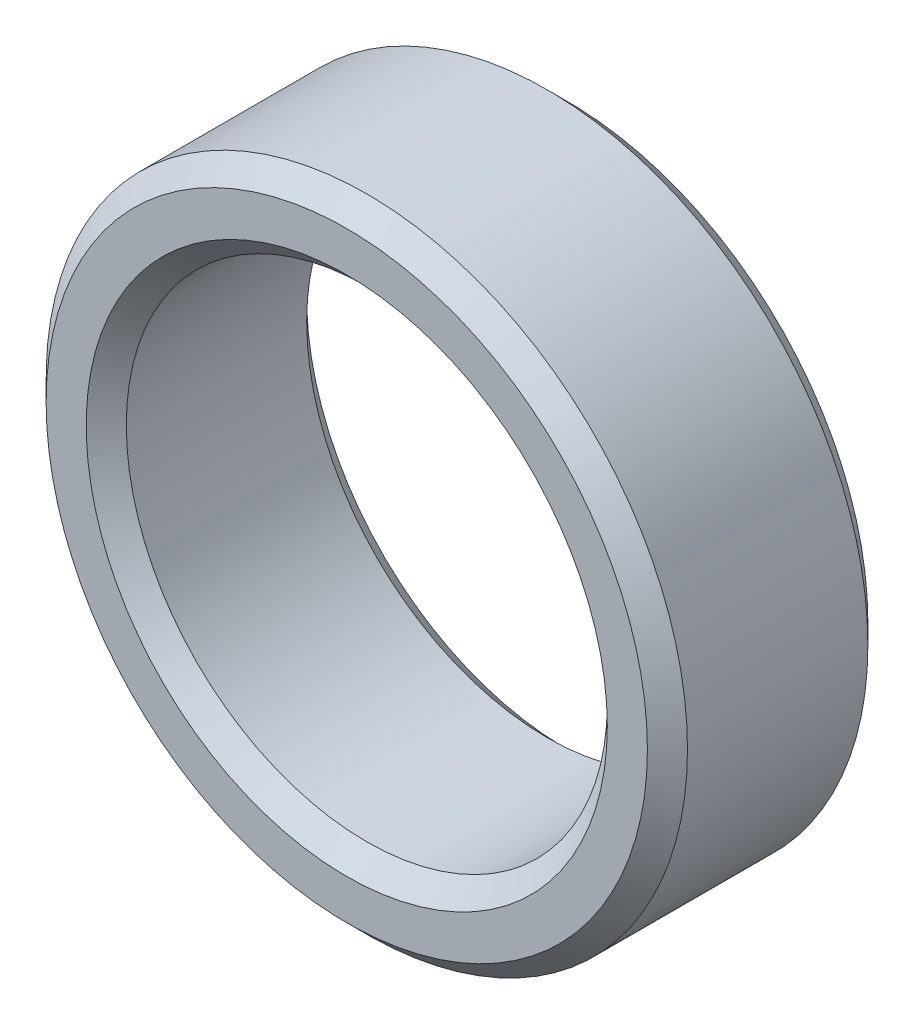
SolidWorks part; units mm, degrees
material "1060 Alloy"
ref_plane "Front Plane" through (0, 0, 0) normal (0, 0, 1) x (1, 0, 0)
ref_plane "Top Plane" through (0, 0, 0) normal (0, 1, 0) x (1, 0, 0)
ref_plane "Right Plane" through (0, 0, 0) normal (1, 0, 0) x (0, 0, -1)
sketch "Sketch1" plane through (0, 0, 0) normal (0, 0, 1) x (1, 0, 0)
  circle A0 centre (0, 0) radius 8
  circle A1 centre (0, 0) radius 6
  dimension "D1" = 16
  dimension "D2" = 12
extrude "Boss-Extrude1" add sketch "Sketch1" along normal blind 5.5
chamfer "Chamfer1" distance 0.5 angle 45 4 edges at (6, 0, 5.5) (8, 0, 5.5) (6, 0, 0) (8, 0, 0)
